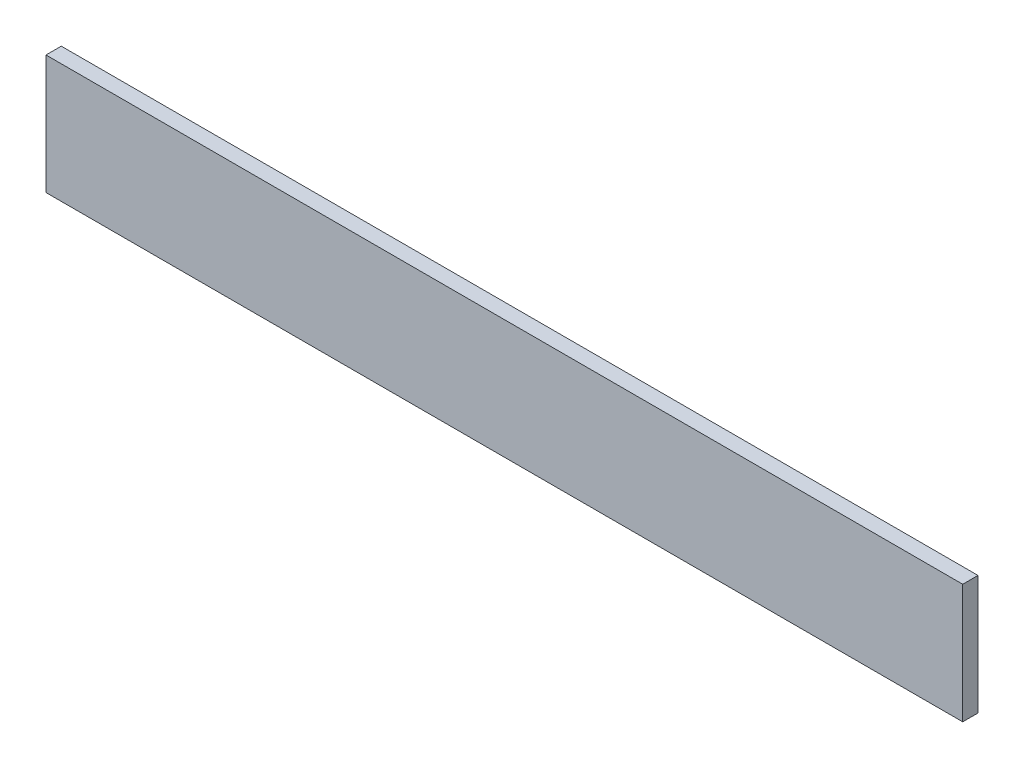
SolidWorks part; units mm, degrees
ref_plane "Plan de face" through (0, 0, 0) normal (0, 0, 1) x (1, 0, 0)
ref_plane "Plan de dessus" through (0, 0, 0) normal (0, 1, 0) x (1, 0, 0)
ref_plane "Plan de droite" through (0, 0, 0) normal (1, 0, 0) x (0, 0, -1)
sketch "Esquisse1" plane through (0, 0, 0) normal (0, 0, 1) x (1, 0, 0)
  line L1 (0, 0) -> (600, 0)
  line L2 (0, 0) -> (0, 78)
  line L3 (0, 78) -> (600, 78)
  line L4 (600, 0) -> (600, 78)
  dimension "D1" = 600
  dimension "D2" = 78
extrude "Boss.-Extru.1" add sketch "Esquisse1" along normal blind 10
